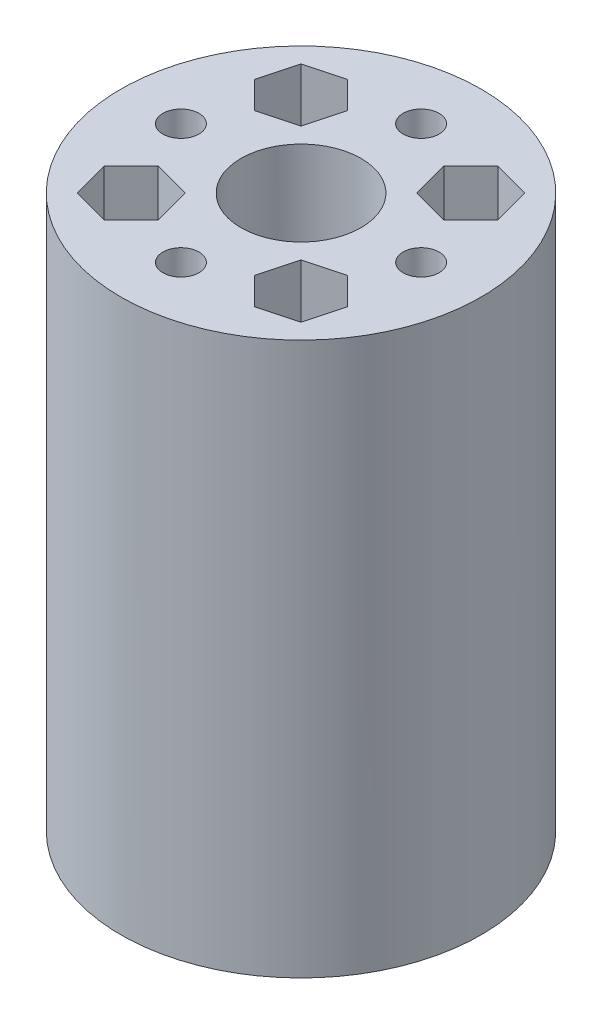
SolidWorks part; units mm, degrees
ref_plane "前视基准面" through (0, 0, 0) normal (0, 0, 1) x (1, 0, 0)
ref_plane "上视基准面" through (0, 0, 0) normal (0, 1, 0) x (1, 0, 0)
ref_plane "右视基准面" through (0, 0, 0) normal (1, 0, 0) x (0, 0, -1)
sketch "草图1" plane through (0, 0, 0) normal (0, 1, 0) x (1, 0, 0)
  circle A0 centre (-5.3729, -8.9317) radius 15
  circle A1 centre (-22.3729, 8.0683) radius 2.1
  circle A5 centre (-5.3729, -8.9317) radius 5
  circle A6 centre (-22.3729, 8.0683) radius 3.5
  dimension "D4" = 4.2
  dimension "D8" = 10
  dimension "D9" = 7
extrude "凸台-拉伸4" add sketch "草图1" along normal blind 3
sketch "草图5" plane through (0, 0, 0) normal (0, 1, 0) x (1, 0, 0)
  line L0 (-22.3729, 4.5683) -> (-10.3729, -8.9317)
  line L1 (-5.3729, -3.9317) -> (-18.8729, 8.0683)
  line L2 (-18.8729, 8.0683) -> (-22.3729, 4.5683)
  line L3 (-10.3729, -8.9317) -> (-10.3729, -3.9317)
  line L4 (-10.3729, -3.9317) -> (-5.3729, -3.9317)
  circle A0 centre (-22.3729, 8.0683) radius 3.5 construction
  circle A1 centre (-5.3729, -8.9317) radius 5 construction
extrude "凸台-拉伸5" add sketch "草图5" along normal blind 3
pattern_circular "阵列(圆周)2" count 4 over 360 about axis through (-5.3729, 0, 8.9317) along (0, 1, 0) of "凸台-拉伸5"
sketch "草图6" plane through (0, 3, 0) normal (0, 1, 0) x (1, 0, 0)
  circle A0 centre (11.6271, 8.0683) radius 2.1
  circle A1 centre (11.6271, 8.0683) radius 3.5
  dimension "D2" = 4.2
  dimension "D3" = 7
extrude "凸台-拉伸6" add sketch "草图6" against normal blind 3
pattern_circular "阵列(圆周)3" count 4 over 360 about axis through (-5.3729, 0, 8.9317) along (0, 1, 0) of "凸台-拉伸6"
sketch "草图7" plane through (0, 0, 0) normal (0, -1, 0) x (1, 0, 0)
  circle A0 centre (-5.3729, 8.9317) radius 15
  circle A1 centre (-5.3729, 8.9317) radius 5
extrude "凸台-拉伸7" add sketch "草图7" along normal blind 46
sketch "草图8" plane through (0, -46, 0) normal (0, -1, 0) x (1, 0, 0)
  line L4 (3.9435, 18.2482) -> (0.8763, 19.07)
  line L5 (0.8763, 19.07) -> (-1.3691, 16.8247)
  line L6 (-1.3691, 16.8247) -> (-0.5472, 13.7574)
  line L7 (-0.5472, 13.7574) -> (2.52, 12.9356)
  line L8 (2.52, 12.9356) -> (4.7654, 15.1809)
  line L9 (4.7654, 15.1809) -> (3.9435, 18.2482)
  circle A3 centre (1.6982, 16.0028) radius 2.75 construction
  dimension "D1" = 5.5
sketch "草图9" plane through (0, 3, 0) normal (0, 1, 0) x (1, 0, 0)
  line L0 (0.8763, -19.07) -> (-1.3691, -16.8247) construction
  line L1 (3.9435, -18.2482) -> (0.8763, -19.07) construction
  line L2 (4.7654, -15.1809) -> (3.9435, -18.2482) construction
  line L3 (2.52, -12.9356) -> (4.7654, -15.1809) construction
  line L4 (-0.5472, -13.7574) -> (2.52, -12.9356) construction
  line L5 (-1.3691, -16.8247) -> (-0.5472, -13.7574) construction
  line L6 (0.8763, -19.07) -> (-1.3691, -16.8247)
  line L7 (3.9435, -18.2482) -> (0.8763, -19.07)
  line L8 (4.7654, -15.1809) -> (3.9435, -18.2482)
  line L9 (2.52, -12.9356) -> (4.7654, -15.1809)
  line L10 (-0.5472, -13.7574) -> (2.52, -12.9356)
  line L11 (-1.3691, -16.8247) -> (-0.5472, -13.7574)
extrude "切除-拉伸1" cut sketch "草图9" against normal blind 46
pattern_circular "阵列(圆周)4" count 4 over 360 about axis through (-5.3729, 0, 8.9317) along (0, 1, 0) of "切除-拉伸1"
sketch "草图11" plane through (0, -43, 0) normal (0, 1, 0) x (1, 0, 0)
  circle A0 centre (1.6982, -1.8607) radius 1.5
  dimension "D1" = 3
extrude "切除-拉伸2" cut sketch "草图11" against normal blind 3
pattern_circular "阵列(圆周)5" count 4 over 360 about axis through (-5.3729, 0, 8.9317) along (0, 1, 0) of "切除-拉伸2"
sketch "草图12" plane through (0, 3, 0) normal (0, 1, 0) x (1, 0, 0)
  line L0 (15.1271, 8.0683) -> (15.1271, -25.9317)
  line L1 (15.1271, -25.9317) -> (11.6271, -22.4317)
  line L2 (11.6271, -22.4317) -> (11.6271, 4.5683)
  line L3 (11.6271, 4.5683) -> (15.1271, 8.0683)
  arc A0 (11.6271, 4.5683) -> (8.1271, 8.0683) centre (11.6271, 8.0683) ccw construction
  arc A1 (8.1271, -25.9317) -> (11.6271, -22.4317) centre (11.6271, -25.9317) ccw construction
extrude "凸台-拉伸8" add sketch "草图12" against normal blind 3
sketch "草图13" plane through (0, 3, 0) normal (0, 1, 0) x (1, 0, 0)
  line L0 (11.6271, 11.5683) -> (-22.3729, 11.5683)
  line L1 (-22.3729, 11.5683) -> (-18.8729, 8.0683)
  line L2 (-18.8729, 8.0683) -> (8.1271, 8.0683)
  line L3 (8.1271, 8.0683) -> (11.6271, 11.5683)
  arc A0 (15.1271, 8.0683) -> (8.1271, 8.0683) centre (11.6271, 8.0683) ccw construction
  arc A1 (-18.8729, 8.0683) -> (-22.3729, 4.5683) centre (-22.3729, 8.0683) ccw construction
extrude "凸台-拉伸9" add sketch "草图13" against normal blind 3
sketch "草图14" plane through (0, 3, 0) normal (0, 1, 0) x (1, 0, 0)
  line L0 (-25.8729, 8.0683) -> (-25.8729, -25.9317)
  line L1 (-25.8729, -25.9317) -> (-22.3729, -22.4317)
  line L2 (-22.3729, -22.4317) -> (-22.3729, 4.5683)
  line L3 (-22.3729, 4.5683) -> (-25.8729, 8.0683)
  arc A0 (-22.3729, 11.5683) -> (-22.3729, 4.5683) centre (-22.3729, 8.0683) ccw construction
  arc A1 (-22.3729, -22.4317) -> (-18.8729, -25.9317) centre (-22.3729, -25.9317) ccw construction
extrude "凸台-拉伸10" add sketch "草图14" against normal blind 3
sketch "草图15" plane through (0, 3, 0) normal (0, 1, 0) x (1, 0, 0)
  line L0 (-22.3729, -29.4317) -> (11.6271, -29.4317)
  line L1 (11.6271, -29.4317) -> (8.1271, -25.9317)
  line L2 (8.1271, -25.9317) -> (-18.8729, -25.9317)
  line L3 (-18.8729, -25.9317) -> (-22.3729, -29.4317)
  arc A0 (-25.8729, -25.9317) -> (-18.8729, -25.9317) centre (-22.3729, -25.9317) ccw construction
  arc A1 (8.1271, -25.9317) -> (15.1271, -25.9317) centre (11.6271, -25.9317) ccw construction
extrude "凸台-拉伸11" add sketch "草图15" against normal blind 3
sketch "草图16" plane through (0, 0, 0) normal (0, -1, 0) x (1, 0, 0)
  line L0 (-10.7479, -4.1933) -> (0.0021, -4.1933)
  line L1 (0.0021, -4.1933) -> (5.1636, -8.0683)
  line L2 (-18.8729, -8.0683) -> (8.1271, -8.0683) construction
  line L3 (4.9912, -11.5683) -> (0.0021, -14.9433)
  line L4 (11.6271, -11.5683) -> (-22.3729, -11.5683) construction
  line L5 (-7.5725, -9.5683) -> (-9.1602, -6.8183)
  line L6 (-9.1602, -6.8183) -> (-12.3356, -6.8183)
  line L7 (-12.3356, -6.8183) -> (-13.9233, -9.5683)
  line L8 (-13.9233, -9.5683) -> (-12.3356, -12.3183)
  line L9 (-12.3356, -12.3183) -> (-9.1602, -12.3183)
  line L10 (-9.1602, -12.3183) -> (-7.5725, -9.5683)
  line L11 (3.1775, -9.5683) -> (1.5898, -6.8183)
  line L12 (1.5898, -6.8183) -> (-1.5856, -6.8183)
  line L13 (-1.5856, -6.8183) -> (-3.1733, -9.5683)
  line L14 (-3.1733, -9.5683) -> (-1.5856, -12.3183)
  line L15 (-1.5856, -12.3183) -> (1.5898, -12.3183)
  line L16 (1.5898, -12.3183) -> (3.1775, -9.5683)
  line L17 (0.0021, -14.9433) -> (-10.7479, -14.9433)
  line L18 (-10.7479, -14.9433) -> (-15.7369, -11.5683)
  line L19 (-15.7369, -11.5683) -> (-15.9094, -8.0683)
  line L20 (-15.9094, -8.0683) -> (-10.7479, -4.1933)
  line L21 (4.9912, -11.5683) -> (5.1636, -8.0683)
  circle A0 centre (-10.7479, -9.5683) radius 2.75 construction
  circle A2 centre (0.0021, -9.5683) radius 2.75 construction
  dimension "D4" = 5.5
  dimension "D5" = 5.5
sketch "草图17" plane through (0, 0, 0) normal (0, -1, 0) x (1, 0, 0)
  line L1 (-7.5725, -9.5683) -> (-9.1602, -6.8183)
  line L2 (-9.1602, -6.8183) -> (-12.3356, -6.8183)
  line L3 (-12.3356, -6.8183) -> (-13.9233, -9.5683)
  line L4 (-13.9233, -9.5683) -> (-12.3356, -12.3183)
  line L5 (-12.3356, -12.3183) -> (-9.1602, -12.3183)
  line L6 (-9.1602, -12.3183) -> (-7.5725, -9.5683)
  line L7 (3.1775, -9.5683) -> (1.5898, -6.8183)
  line L8 (1.5898, -6.8183) -> (-1.5856, -6.8183)
  line L9 (-1.5856, -6.8183) -> (-3.1733, -9.5683)
  line L10 (-3.1733, -9.5683) -> (-1.5856, -12.3183)
  line L11 (-1.5856, -12.3183) -> (1.5898, -12.3183)
  line L12 (1.5898, -12.3183) -> (3.1775, -9.5683)
  circle A0 centre (-10.7479, -9.5683) radius 2.75 construction
  circle A1 centre (0.0021, -9.5683) radius 2.75 construction
extrude "凸台-拉伸13" add sketch "草图16" against normal blind 3
sketch "草图18" plane through (0, 0, 0) normal (0, -1, 0) x (1, 0, 0)
  line L1 (-7.5725, -9.5683) -> (-9.1602, -6.8183)
  line L2 (-9.1602, -6.8183) -> (-12.3356, -6.8183)
  line L3 (-12.3356, -6.8183) -> (-13.9233, -9.5683)
  line L4 (-13.9233, -9.5683) -> (-12.3356, -12.3183)
  line L5 (-12.3356, -12.3183) -> (-9.1602, -12.3183)
  line L6 (-9.1602, -12.3183) -> (-7.5725, -9.5683)
  line L7 (3.1775, -9.5683) -> (1.5898, -6.8183)
  line L8 (1.5898, -6.8183) -> (-1.5856, -6.8183)
  line L9 (-1.5856, -6.8183) -> (-3.1733, -9.5683)
  line L10 (-3.1733, -9.5683) -> (-1.5856, -12.3183)
  line L11 (-1.5856, -12.3183) -> (1.5898, -12.3183)
  line L12 (1.5898, -12.3183) -> (3.1775, -9.5683)
  circle A0 centre (-10.7479, -9.5683) radius 2.75 construction
  circle A1 centre (0.0021, -9.5683) radius 2.75 construction
extrude "凸台-拉伸14" add sketch "草图18" against normal blind 3
extrude "切除-拉伸3" cut sketch "草图17" against normal blind 2.5
sketch "草图19" plane through (0, 2.5, 0) normal (0, -1, 0) x (1, 0, 0)
  circle A0 centre (0.0021, -9.5683) radius 1.5
  dimension "D1" = 3
extrude "切除-拉伸4" cut sketch "草图19" against normal blind 2.5
sketch "草图20" plane through (0, 2.5, 0) normal (0, -1, 0) x (1, 0, 0)
  circle A0 centre (-10.7479, -9.5683) radius 1.5
  dimension "D1" = 3
extrude "切除-拉伸5" cut sketch "草图20" against normal blind 2.5
sketch "草图21" plane through (0, 0, 0) normal (0, 1, 0) x (1, 0, 0)
  circle A0 centre (59.6655, -8.9317) radius 15
  circle A1 centre (59.6655, -8.9317) radius 5
  dimension "D1" = 30
  dimension "D2" = 10
extrude "凸台-拉伸15" add sketch "草图21" along normal blind 3 separate body
sketch "草图22" plane through (0, 0, 0) normal (0, -1, 0) x (1, 0, 0)
  circle A0 centre (59.6655, 18.9317) radius 1.5
  dimension "D2" = 3
extrude "切除-拉伸6" cut sketch "草图22" against normal blind 3
pattern_circular "阵列(圆周)6" count 4 over 360 about axis through (59.6655, 0, 8.9317) along (0, 1, 0) of "切除-拉伸6"
extrude "凸台-拉伸16" add sketch "草图8" along normal blind 3
sketch "草图24" plane through (0, -49, 0) normal (0, -1, 0) x (1, 0, 0)
  line L1 (4.7654, 15.1809) -> (3.9435, 18.2482)
  line L2 (3.9435, 18.2482) -> (0.8763, 19.07)
  line L3 (0.8763, 19.07) -> (-1.3691, 16.8247)
  line L4 (-1.3691, 16.8247) -> (-0.5472, 13.7574)
  line L5 (-0.5472, 13.7574) -> (2.52, 12.9356)
  line L6 (2.52, 12.9356) -> (4.7654, 15.1809)
  circle A0 centre (1.6982, 16.0028) radius 2.75 construction
extrude "切除-拉伸7" cut sketch "草图24" against normal blind 3
sketch "草图25" plane through (0, 0, 0) normal (0, -1, 0) x (1, 0, 0)
  circle A0 centre (59.6655, 8.9317) radius 15
  circle A1 centre (59.6655, 8.9317) radius 5
extrude "凸台-拉伸17" add sketch "草图25" along normal blind 43
sketch "草图27" plane through (0, 3, 0) normal (0, 1, 0) x (1, 0, 0)
  circle A0 centre (59.6655, 1.0683) radius 1.5
  circle A1 centre (69.6655, -8.9317) radius 1.5
  circle A2 centre (59.6655, -18.9317) radius 1.5
  circle A3 centre (49.6655, -8.9317) radius 1.5
extrude "切除-拉伸8" cut sketch "草图27" against normal blind 46
sketch "草图28" plane through (0, -43, 0) normal (0, -1, 0) x (1, 0, 0)
  circle A0 centre (59.6655, 18.9317) radius 2.75
  circle A1 centre (49.6655, 8.9317) radius 2.75
  circle A2 centre (59.6655, -1.0683) radius 2.75
  circle A3 centre (69.6655, 8.9317) radius 2.75
  dimension "D1" = 5.5
  dimension "D2" = 5.5
  dimension "D3" = 5.5
  dimension "D4" = 5.5
extrude "切除-拉伸9" cut sketch "草图28" against normal blind 43
sketch "草图29" plane through (0, 3, 0) normal (0, 1, 0) x (1, 0, 0)
  circle A0 centre (66.7366, -1.8607) radius 1.5
  dimension "D2" = 3
extrude "切除-拉伸10" cut sketch "草图29" against normal blind 46
pattern_circular "阵列(圆周)7" count 4 over 360 about axis through (59.6655, 0, 8.9317) along (0, 1, 0) of "切除-拉伸10"
sketch "草图30" plane through (0, 3, 0) normal (0, 1, 0) x (1, 0, 0)
  line L2 (64.4912, -4.106) -> (67.5585, -4.9279)
  line L3 (67.5585, -4.9279) -> (69.8038, -2.6825)
  line L4 (69.8038, -2.6825) -> (68.982, 0.3847)
  line L5 (68.982, 0.3847) -> (65.9148, 1.2066)
  line L6 (65.9148, 1.2066) -> (63.6694, -1.0388)
  line L7 (63.6694, -1.0388) -> (64.4912, -4.106)
  circle A0 centre (66.7366, -1.8607) radius 2.75 construction
  dimension "D1" = 5.5
extrude "切除-拉伸11" cut sketch "草图30" against normal blind 43
pattern_circular "阵列(圆周)8" count 4 over 360 about axis through (59.6655, 0, 8.9317) along (0, 1, 0) of "切除-拉伸11"
sketch "草图31" plane through (0, 3, 0) normal (0, 1, 0) x (1, 0, 0)
  circle A0 centre (-6.3011, -7.4597) radius 35.8624
extrude "切除-拉伸12" cut sketch "草图31" against normal blind 100
